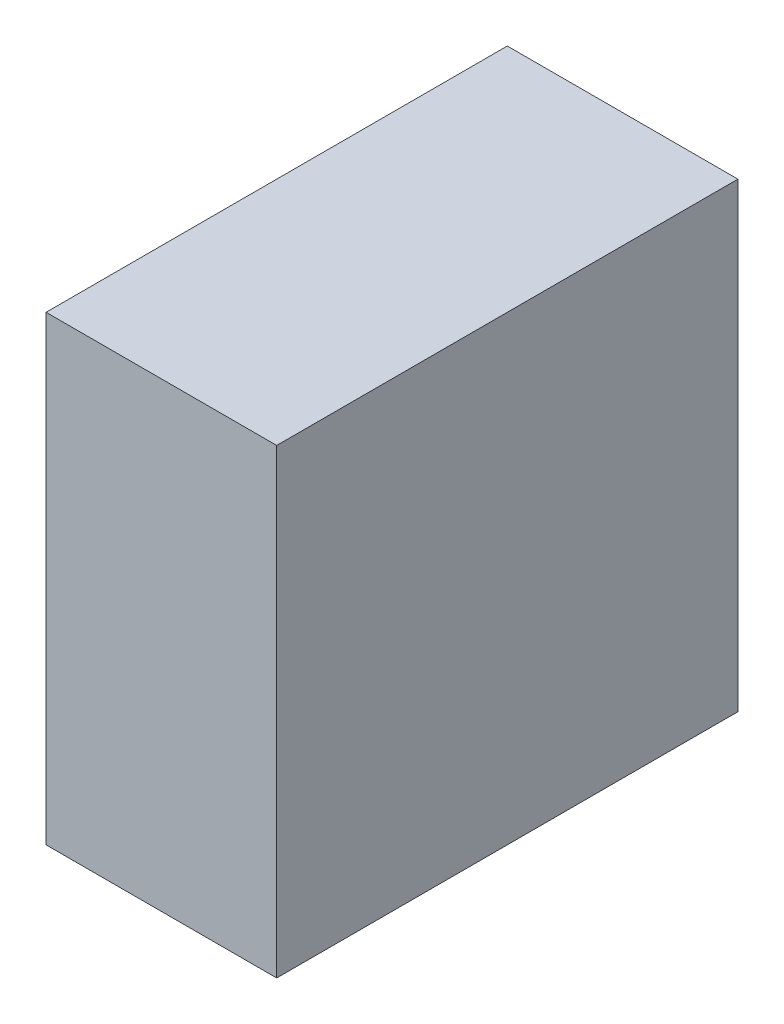
SolidWorks part; units mm, degrees
ref_plane "Front Plane" through (0, 0, 0) normal (0, 0, 1) x (1, 0, 0)
ref_plane "Top Plane" through (0, 0, 0) normal (0, 1, 0) x (1, 0, 0)
ref_plane "Right Plane" through (0, 0, 0) normal (1, 0, 0) x (0, 0, -1)
sketch "Sketch1" plane through (0, 0, 0) normal (0, 1, 0) x (1, 0, 0)
  line L1 (-18.8472, 22.0734) -> (6.5528, 22.0734)
  line L2 (-18.8472, 22.0734) -> (-18.8472, -28.7266)
  line L3 (-18.8472, -28.7266) -> (6.5528, -28.7266)
  line L4 (6.5528, 22.0734) -> (6.5528, -28.7266)
  dimension "D1" = 25.4
  dimension "D2" = 50.8
extrude "Boss-Extrude1" add sketch "Sketch1" along normal blind 50.8
